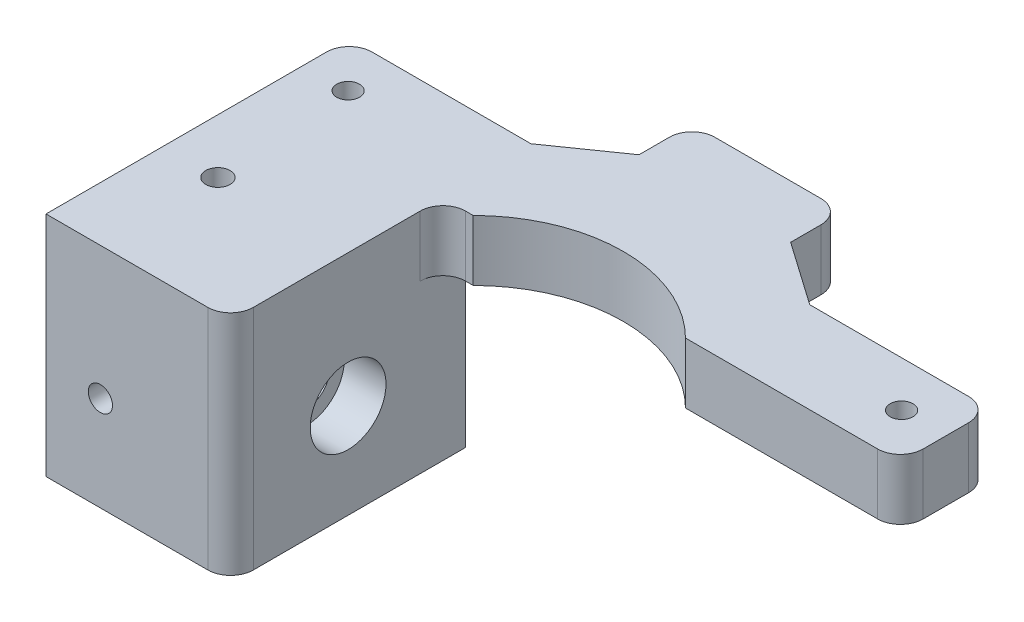
SolidWorks part; units mm, degrees
ref_plane "Front Plane" through (0, 0, 0) normal (0, 0, 1) x (1, 0, 0)
ref_plane "Top Plane" through (0, 0, 0) normal (0, 1, 0) x (1, 0, 0)
ref_plane "Right Plane" through (0, 0, 0) normal (1, 0, 0) x (0, 0, -1)
sketch "Sketch1" plane through (0, 0, 0) normal (0, 1, 0) x (1, 0, 0)
  point P0 (19.9354, 20.5827)
  line B0 (39.209, 44.4444) -> (22.0404, 42.2474)
  line B1 (45.8541, 73.4809) -> (45.8541, 51.994)
  line B2 (42.0529, 77.2821) -> (-35.0361, 77.2821)
  line B3 (-38.8372, 73.4809) -> (-38.8372, 51.994)
  line B4 (-32.1921, 44.4444) -> (-15.0236, 42.2474)
  arc B5 (19.8482, 42.7521) -> (-12.8313, 42.7521) centre (3.5084, 38.4289) ccw
  circle B6 centre (-16.4916, 46.356) radius 2.5
  circle B7 centre (-32.9916, 71.4109) radius 2.5
  circle B8 centre (40.0084, 71.4109) radius 2.5
  circle B9 centre (23.5084, 46.356) radius 2.5
  arc B10 (39.209, 44.4444) -> (45.8541, 51.994) centre (38.2429, 51.994) ccw
  arc B11 (-35.0361, 77.2821) -> (-38.8372, 73.4809) centre (-35.0361, 73.4809) ccw
  arc B12 (-38.8372, 51.994) -> (-32.1921, 44.4444) centre (-31.2261, 51.994) ccw
sketch_block_instance "ps3_eye_screws-1"
sketch_block "ps3_eye_screws"
sketch "Sketch2" plane through (0, 0, 0) normal (0, 1, 0) x (1, 0, 0)
  line L0 (3.5084, 38.4024) -> (3.5084, 55.3309) construction
  line L4 (-38.8372, 64.4109) -> (-14.8764, 64.4109)
  line L5 (-32.9916, 71.4109) -> (40.0084, 71.4109) construction
  line L6 (-32.9916, 71.4109) -> (-32.9916, 58.4109) construction
  line L7 (-32.9916, 58.4109) -> (40.0084, 58.4109) construction
  line L8 (40.0084, 71.4109) -> (40.0084, 58.4109) construction
  line L9 (-38.8372, 73.4809) -> (-38.8372, 51.994) construction
  line L10 (-14.8764, 64.4109) -> (-6.4916, 70.2821)
  line L11 (-6.4916, 70.2821) -> (-6.4916, 77.2821)
  line L12 (42.0529, 77.2821) -> (-35.0361, 77.2821) construction
  line L13 (-6.4916, 77.2821) -> (13.5084, 77.2821)
  line L14 (13.5084, 77.2821) -> (13.5084, 70.2821)
  line L15 (13.5084, 70.2821) -> (21.8933, 64.4109)
  line L16 (21.8933, 64.4109) -> (45.8541, 64.4109)
  line L17 (45.8541, 73.4809) -> (45.8541, 51.994) construction
  line L18 (45.8541, 64.4109) -> (45.8541, 52.4109)
  line L19 (45.8541, 52.4109) -> (17.5084, 52.4109)
  line L20 (-10.4916, 52.4109) -> (-38.8372, 52.4109)
  line L21 (-38.8372, 52.4109) -> (-38.8372, 64.4109)
  line L22 (3.5084, 55.3309) -> (3.5084, 77.2821) construction
  line L23 (-6.4916, 70.2821) -> (13.5084, 70.2821) construction
  line L24 (-32.9916, 58.4109) -> (-38.8372, 58.4109) construction
  line L25 (40.0084, 58.4109) -> (45.8541, 58.4109) construction
  circle A2 centre (-32.9916, 58.4109) radius 1.5
  circle A3 centre (40.0084, 58.4109) radius 1.5
  arc A4 (19.8482, 42.7521) -> (-12.8313, 42.7521) centre (3.5084, 38.4289) ccw construction
  arc A5 (-10.4916, 52.4109) -> (17.5084, 52.4109) centre (3.5084, 38.4024) cw
  point P27 (8.08, 39.4837)
  point P33 (3.5084, 42.9446)
  point P34 (3.5084, 38.4024)
  dimension "D1" = 3
  dimension "D7" = 28
  dimension "D8" = 19.805
  dimension "D2" = 13
  dimension "D3" = 145
  dimension "D4" = 145
  dimension "D5" = 20
  dimension "D6" = 12
  dimension "D9" = 7
extrude "Boss-Extrude1" add sketch "Sketch2" along normal blind 8
ref_plane "Plane1" through (0, 8, 0) normal (0, -1, 0) x (-1, 0, 0)
sketch "Sketch11" plane through (0, 8, 0) normal (0, -1, 0) x (-1, 0, 0)
  line L1 (14.4916, 55.4109) -> (38.8372, 55.4109)
  line L2 (14.4916, 55.4109) -> (14.4916, 24.4109)
  line L3 (14.4916, 24.4109) -> (38.8372, 24.4109)
  line L4 (38.8372, 55.4109) -> (38.8372, 24.4109)
  line L5 (38.8372, 73.4809) -> (38.8372, 51.994) construction
  circle A0 centre (32.9916, 58.4109) radius 1.5 construction
  point P6 (38.8372, 52.4109)
  point P8 (0, 0)
  point P9 (38.8372, 52.4109)
  point P10 (38.8372, 55.4109)
  dimension "D2" = 3
  dimension "D1" = 5
  dimension "D3" = 31
extrude "Boss-Extrude4" add sketch "Sketch11" along normal blind 30
sketch "Sketch12" plane through (-38.8372, 0, 0) normal (-1, 0, 0) x (0, 0, 1)
  line L0 (-24.4109, -22) -> (-55.4109, -22) construction
  line L1 (-52.4109, -22) -> (-27.4109, -22)
  line L2 (-52.4109, -22) -> (-52.4109, 3)
  line L3 (-52.4109, 3) -> (-27.4109, 3)
  line L4 (-27.4109, -22) -> (-27.4109, 3)
  line L5 (-55.4109, -22) -> (-55.4109, 0) construction
  dimension "D1" = 25
  dimension "D2" = 25
  dimension "D3" = 3
extrude "Cut-Extrude7" cut sketch "Sketch12" against normal offset from surface (14.3456 mm away) 10 up to face at (-14.4916, -4.6667, -44.0776)
sketch "Sketch13" plane through (-14.4916, 0, 0) normal (1, 0, 0) x (0, 0, -1)
  line L0 (52.4109, -22) -> (27.4109, 3) construction
  circle A0 centre (39.9109, -9.5) radius 3.1
  dimension "D1" = 6.2
extrude "Cut-Extrude8" cut sketch "Sketch13" against normal up to next
sketch "Sketch14" plane through (-14.4916, 0, 0) normal (1, 0, 0) x (0, 0, -1)
  circle A0 centre (39.9109, -9.5) radius 5
  dimension "D1" = 10
extrude "Cut-Extrude9" cut sketch "Sketch14" against normal blind 5.5
sketch "Sketch15" plane through (0, 0, -24.4109) normal (0, 0, 1) x (1, 0, 0)
  line L0 (-31.6644, -22) -> (-31.6644, 3) construction
  line L1 (-24.4916, 3) -> (-38.8372, 3) construction
  line L2 (-14.4916, -22) -> (-38.8372, -22) construction
  circle A0 centre (-31.6644, -9.5) radius 1.6
  point P6 (-31.6644, 3)
  point P9 (-34.4877, -22)
  dimension "D1" = 3.2
extrude "Cut-Extrude10" cut sketch "Sketch15" against normal blind 5.5
sketch "Sketch16" plane through (0, 8, 0) normal (0, 1, 0) x (1, 0, 0)
  line L0 (-31.6644, 52.4109) -> (-31.6644, 27.4109) construction
  line L1 (-24.4916, 52.4109) -> (-38.8372, 52.4109) construction
  line L2 (-24.4916, 27.4109) -> (-38.8372, 27.4109) construction
  circle A0 centre (-31.6644, 39.9109) radius 1.6
  dimension "D1" = 3.2
extrude "Cut-Extrude11" cut sketch "Sketch16" against normal up to next contours A0
sketch "Sketch17" plane through (0, 0, 0) normal (0, -1, 0) x (1, 0, 0)
  line L0 (-38.8372, -55.4109) -> (-14.4916, -55.4109) construction
  line L1 (-31.2595, -61.4109) -> (-29.5275, -58.4109)
  line L2 (-29.5275, -58.4109) -> (-31.2595, -55.4109)
  line L3 (-31.2595, -55.4109) -> (-34.7236, -55.4109)
  line L4 (-34.7236, -55.4109) -> (-36.4557, -58.4109)
  line L5 (-36.4557, -58.4109) -> (-34.7236, -61.4109)
  line L6 (-34.7236, -61.4109) -> (-31.2595, -61.4109)
  line L8 (38.2764, -61.4109) -> (41.7405, -61.4109)
  line L9 (41.7405, -61.4109) -> (43.4725, -58.4109)
  line L10 (43.4725, -58.4109) -> (41.7405, -55.4109)
  line L11 (41.7405, -55.4109) -> (38.2764, -55.4109)
  line L12 (38.2764, -55.4109) -> (36.5443, -58.4109)
  line L13 (36.5443, -58.4109) -> (38.2764, -61.4109)
  circle A0 centre (-32.9916, -58.4109) radius 3 construction
  circle A1 centre (40.0084, -58.4109) radius 3 construction
extrude "Cut-Extrude12" cut sketch "Sketch17" against normal blind 2.6
fillet "Fillet2" radius 3 7 edges at (-14.4916, 4, -52.4109) (-14.4916, -7, -24.4109) (45.8541, 4, -52.4109) (45.8541, 4, -64.4109) (13.5084, 4, -77.2821) (-6.4916, 4, -77.2821) (-38.8372, 4, -64.4109)
